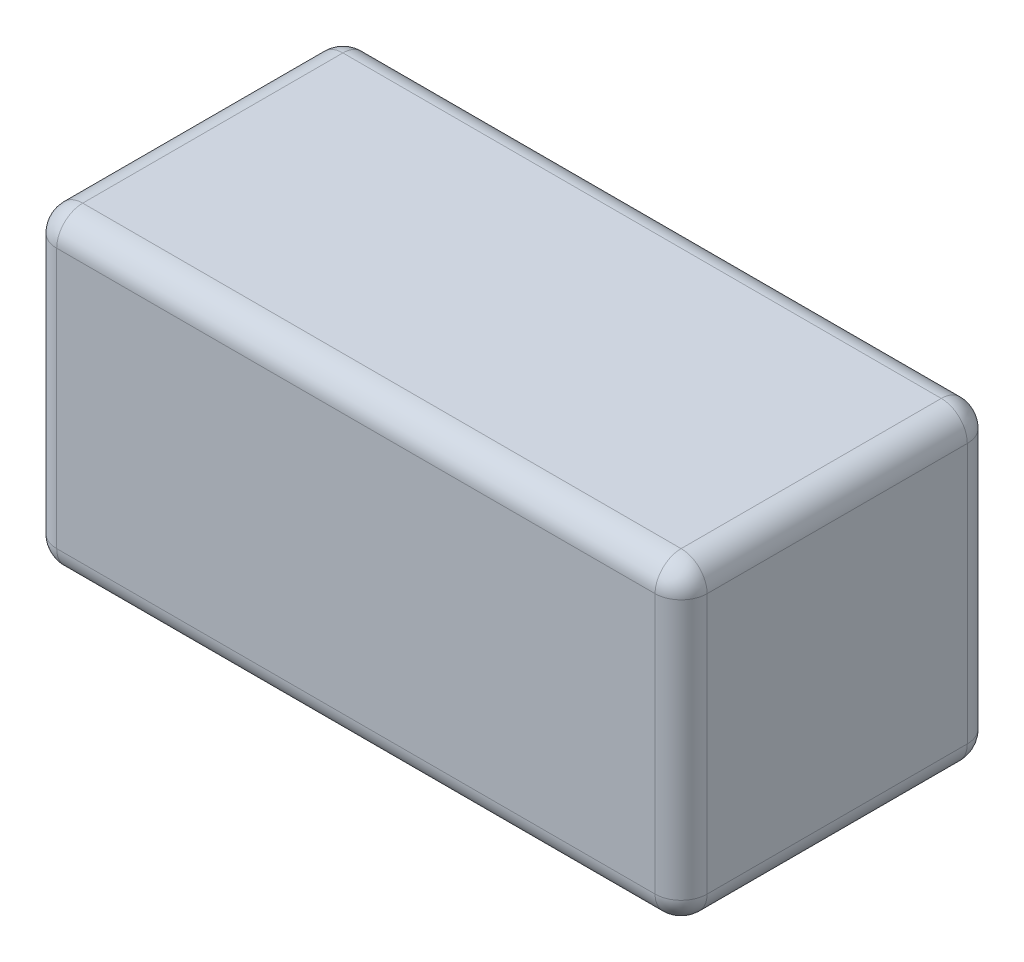
SolidWorks part; units mm, degrees
material "自定义塑料"
ref_plane "前视基准面" through (0, 0, 0) normal (0, 0, 1) x (1, 0, 0)
ref_plane "上视基准面" through (0, 0, 0) normal (0, 1, 0) x (1, 0, 0)
ref_plane "右视基准面" through (0, 0, 0) normal (1, 0, 0) x (0, 0, -1)
sketch "草图1" plane through (0, 0, 0) normal (0, 1, 0) x (1, 0, 0)
  line L1 (-25, 12) -> (25, 12)
  line L2 (-25, 12) -> (-25, -12)
  line L3 (-25, -12) -> (25, -12)
  line L4 (25, 12) -> (25, -12)
  line L5 (-25, 12) -> (25, -12) construction
  line L6 (-25, -12) -> (25, 12) construction
  point P0 (0, 0)
  dimension "D1" = 50
  dimension "D2" = 24
extrude "凸台-拉伸1" add sketch "草图1" along normal blind 24
fillet "圆角1" radius 2 12 edges at (-25, 0, 0) (-25, 12, 12) (-25, 24, 0) (-25, 12, -12) (25, 0, 0) (25, 12, 12) (25, 24, 0) (25, 12, -12) (0, 0, -12) (0, 24, -12) (0, 0, 12) (0, 24, 12)
